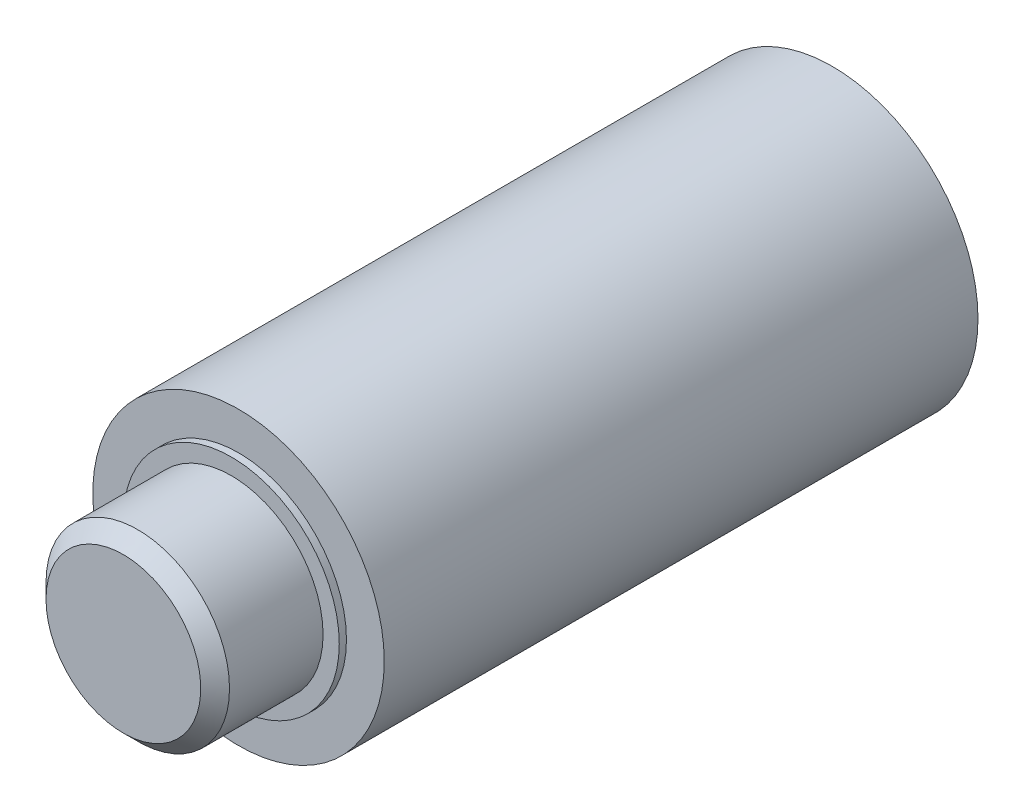
SolidWorks part; units mm, degrees
ref_plane "Front Plane" through (0, 0, 0) normal (0, 0, 1) x (1, 0, 0)
ref_plane "Top Plane" through (0, 0, 0) normal (0, 1, 0) x (1, 0, 0)
ref_plane "Right Plane" through (0, 0, 0) normal (1, 0, 0) x (0, 0, -1)
sketch "Sketch1" plane through (0, 0, 0) normal (0, 1, 0) x (1, 0, 0)
  line L0 (0, -19.7) -> (0, -6.8)
  line L2 (-3.25, -6.8) -> (-3.25, 0)
  line L3 (-3.25, 0) -> (-4.05, 0)
  line L4 (-4.05, 0) -> (-4.05, -16.5)
  line L5 (-4.05, -16.5) -> (-3, -16.5)
  line L6 (-3, -16.5) -> (-3, -16.7)
  line L7 (-3, -16.7) -> (-2.55, -16.7)
  line L8 (-2.55, -16.7) -> (-2.55, -19.7)
  line L10 (2.55, -16.7) -> (2.55, -19.7) construction
  line L11 (3, -16.7) -> (2.55, -16.7) construction
  line L12 (3, -16.5) -> (3, -16.7) construction
  line L13 (4.05, -16.5) -> (3, -16.5) construction
  line L14 (4.05, 0) -> (4.05, -16.5) construction
  line L15 (3.25, 0) -> (4.05, 0) construction
  line L16 (3.25, -6.8) -> (3.25, 0) construction
  line L17 (-3.25, -6.8) -> (0, -6.8)
  line L18 (0, -6.8) -> (3.25, -6.8) construction
  line L19 (2.55, -19.7) -> (0, -19.7) construction
  line L20 (0, -19.7) -> (-2.55, -19.7)
  dimension "D1" = 3
  dimension "D2" = 0.2
  dimension "D3" = 5.1
  dimension "D4" = 6
  dimension "D5" = 6.5
  dimension "D6" = 8.1
  dimension "D7" = 6.8
  dimension "D8" = 16.5
revolve "Revolve1" add sketch "Sketch1" angle 360 about L0
chamfer "Chamfer1" distance 0.4 angle 45 1 edges at (2.55, 0, 19.7)
sketch "Sketch2" plane through (0, 0, 6.8) normal (0, 0, 1) x (1, 0, 0)
  line L0 (0.525, 3.2073) -> (0.525, -3.2073)
  line L1 (-0.525, -3.2073) -> (-0.525, 3.2073)
  line L2 (-0.525, 0) -> (0.525, 0) construction
  circle A0 centre (0, 0) radius 3.25 construction
  arc A1 (0.525, -3.2073) -> (-0.525, -3.2073) centre (0, 0) cw
  arc A2 (-0.525, 3.2073) -> (0.525, 3.2073) centre (0, 0) cw
  dimension "D1" = 1.05
extrude "Boss-Extrude1" add sketch "Sketch2" against normal blind 1.5
chamfer "Chamfer2" distance 1 distance2 0.05 2 edges at (0.525, 0, 6.8) (-0.525, 0, 6.8)
